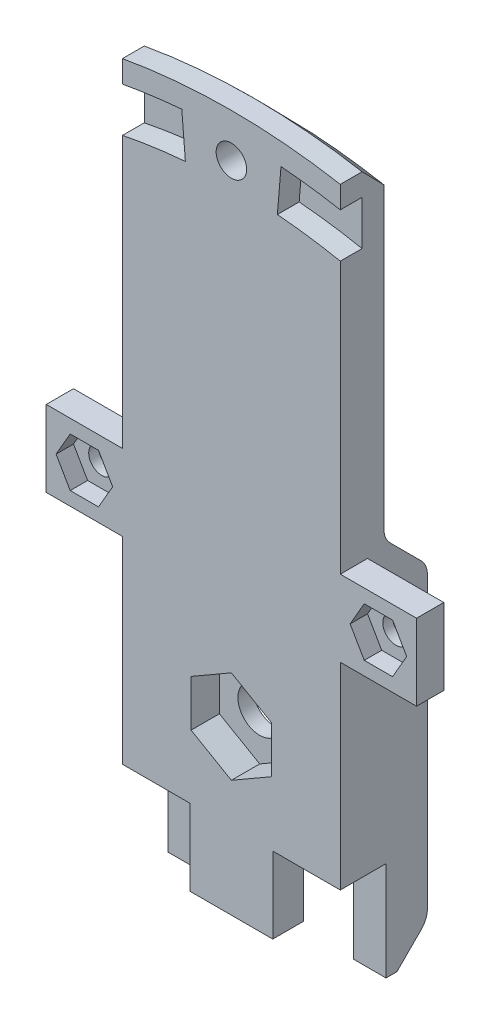
SolidWorks part; units mm, degrees
ref_plane "Front Plane" through (0, 0, 0) normal (0, 0, 1) x (1, 0, 0)
ref_plane "Top Plane" through (0, 0, 0) normal (0, 1, 0) x (1, 0, 0)
ref_plane "Right Plane" through (0, 0, 0) normal (1, 0, 0) x (0, 0, -1)
sketch "Sketch1" plane through (0, 0, 0) normal (0, 0, 1) x (1, 0, 0)
  line L0 (-12.7, -71.2673) -> (-12.7, 71.2673)
  line L1 (12.7, 71.2673) -> (12.7, -71.2673)
  line L2 (-12.7, 0) -> (12.7, 0)
  line L3 (0, 0) -> (0, 40.2261) construction
  arc A0 (-12.7, -71.2673) -> (12.7, -71.2673) centre (0, 0) ccw
  arc A1 (12.7, 71.2673) -> (-12.7, 71.2673) centre (0, 0) ccw
  circle A2 centre (0, 11.43) radius 7.62 construction
  dimension "D1" = 144.78
  dimension "D4" = 15.24
  dimension "D2" = 25.4
  dimension "D3" = 11.43
extrude "Boss-Extrude1" add sketch "Sketch1" along normal blind 5.08 contours L1 A1 L0 L2
sketch "Sketch2" plane through (0, 0, 5.08) normal (0, 0, 1) x (1, 0, 0)
  line L0 (-12.7, 0) -> (12.7, 0) construction
  line L1 (12.7, 71.2673) -> (12.7, 0) construction
  line L2 (-12.7, 0) -> (12.7, 0)
  circle A0 centre (0, 10.16) radius 2.54
extrude "Cut-Extrude1" cut sketch "Sketch2" against normal through all contours A0
sketch "Sketch3" plane through (0, 0, 5.08) normal (0, 0, 1) x (1, 0, 0)
  line L0 (-12.7, 0) -> (-12.7, 71.2673) construction
  line L1 (0, 15.5859) -> (-4.699, 12.873)
  line L2 (-4.699, 12.873) -> (-4.699, 7.447)
  line L3 (-4.699, 7.447) -> (0, 4.7341)
  line L4 (0, 4.7341) -> (4.699, 7.447)
  line L5 (4.699, 7.447) -> (4.699, 12.873)
  line L6 (4.699, 12.873) -> (0, 15.5859)
  circle A0 centre (0, 10.16) radius 4.699 construction
  dimension "D1" = 9.398
extrude "Cut-Extrude2" cut sketch "Sketch3" against normal blind 3.302
sketch "Sketch4" plane through (-12.7, 0, 0) normal (-1, 0, 0) x (0, 0, 1)
  line L0 (-0.7439, 32.1399) -> (-4.3361, 28.5478)
  line L1 (0, 0) -> (0, 71.2673) construction
  line L2 (-5.08, 26.7517) -> (-5.08, -6.9415)
  line L6 (-0.254, -11.5497) -> (-1.524, -11.5497)
  line L7 (0, 33.9359) -> (0, 0)
  line L8 (-1.524, -11.5497) -> (-4.3361, -8.7376)
  line L9 (0, 0) -> (-0.254, 0)
  line L10 (-0.254, 0) -> (-0.254, -11.5497)
  arc A0 (-4.3361, 28.5478) -> (-5.08, 26.7517) centre (-2.54, 26.7517) ccw
  arc A1 (0, 33.9359) -> (-0.7439, 32.1399) centre (-2.54, 33.9359) cw
  arc A2 (-5.08, -6.9415) -> (-4.3361, -8.7376) centre (-2.54, -6.9415) ccw
  point P15 (0, 31.75)
  dimension "D6" = 2.54
  dimension "D7" = 2.54
  dimension "D9" = 2.54
  dimension "D1" = 45
  dimension "D2" = 8.7376
  dimension "D3" = 45
  dimension "D4" = 1.27
  dimension "D5" = 5.08
  dimension "D8" = 33.9359
  dimension "D10" = 0.254
extrude "Boss-Extrude2" add sketch "Sketch4" against normal up to surface (25.4 mm away) up to face at (12.7, 35.6336, 2.54)
sketch "Sketch5" plane through (0, 0, 0) normal (1, 0, 0) x (0, 0, -1)
  line L0 (0, 33.9359) -> (0, -14.8745)
  line L1 (5.08, 24.709) -> (0, 22.86)
  line L2 (0, 22.86) -> (0, 0)
  line L9 (0, 33.9359) -> (0, 71.2673)
  line L10 (0, 71.2673) -> (-5.08, 71.2673)
  line L11 (-5.08, 71.2673) -> (-5.08, 0)
  line L12 (-5.08, 0) -> (0.254, 0)
  line L13 (0.254, 0) -> (0.254, -11.5497)
  line L14 (0.254, -11.5497) -> (1.524, -11.5497)
  line L15 (0.254, -11.5497) -> (1.524, -11.5497)
  line L16 (5.08, -6.9415) -> (5.08, 26.7517)
  line L17 (4.3361, 28.5478) -> (0.7439, 32.1399)
  line L18 (0, 33.9359) -> (0, 71.2673)
  line L19 (0, 71.2673) -> (-5.08, 71.2673)
  line L20 (-5.08, 71.2673) -> (-5.08, 0)
  line L21 (-5.08, 0) -> (0.254, 0)
  line L25 (5.08, -6.9415) -> (5.08, 26.7517)
  line L26 (4.3361, 28.5478) -> (0.7439, 32.1399)
  line L29 (1.524, -11.5497) -> (4.3361, -8.7376)
  line L30 (1.524, -11.5497) -> (4.3361, -8.7376)
  line L31 (0.254, 0) -> (0.254, -11.5497)
  arc A2 (5.08, 26.7517) -> (4.3361, 28.5478) centre (2.54, 26.7517) ccw
  arc A3 (0, 33.9359) -> (0.7439, 32.1399) centre (2.54, 33.9359) ccw
  arc A4 (5.08, 26.7517) -> (4.3361, 28.5478) centre (2.54, 26.7517) ccw
  arc A5 (0, 33.9359) -> (0.7439, 32.1399) centre (2.54, 33.9359) ccw
  arc A7 (4.3361, -8.7376) -> (5.08, -6.9415) centre (2.54, -6.9415) ccw
  arc A8 (4.3361, -8.7376) -> (5.08, -6.9415) centre (2.54, -6.9415) ccw
  dimension "D2" = 70
  dimension "D3" = 22.86
  dimension "D1" = 0
extrude "Cut-Extrude3" cut sketch "Sketch5" against normal mid plane 17.78
chamfer "Chamfer1" distance 2.54 angle 45 1 edges at (0, 72.39, 0)
sketch "Sketch6" plane through (0, 0, 5.08) normal (0, 0, 1) x (1, 0, 0)
  line L0 (-12.7, 0) -> (12.7, 0) construction
  line L1 (-4.826, 0) -> (4.826, 0)
  line L2 (-4.826, 0) -> (-4.826, -8.89)
  line L3 (-4.826, -8.89) -> (4.826, -8.89)
  line L4 (4.826, 0) -> (4.826, -8.89)
  line L5 (-4.826, 0) -> (4.826, -8.89) construction
  line L6 (-4.826, -8.89) -> (4.826, 0) construction
  line L7 (-12.7, -11.5497) -> (-12.7, 0) construction
  line L8 (12.7, 71.2673) -> (12.7, 0) construction
  point P4 (0, -4.445)
extrude "Boss-Extrude3" add sketch "Sketch6" against normal blind 3.556
sketch "Sketch8" plane through (0, 0, 0) normal (0, 0, -1) x (-1, 0, 0)
  line L0 (-0.5228, 37.6298) -> (-0.5228, 106.6362) construction
  line L3 (-4.5278, 41.6168) -> (31.321, 41.6168) construction
  line L4 (-9.4837, 45.8216) -> (17.6963, 45.8216) construction
  line L5 (10.16, 33.9359) -> (10.16, 69.1071) construction
  line L6 (-12.7, 33.9359) -> (12.7, 33.9359) construction
  line L7 (-10.16, 33.9359) -> (-10.16, 69.1071) construction
  line L8 (-12.7, 68.6858) -> (-12.7, 33.9359) construction
  line L9 (12.7, 33.9359) -> (12.7, 68.6858) construction
  line L10 (5.715, 33.9359) -> (5.715, 69.6158) construction
  line L11 (-5.715, 69.6158) -> (-5.715, 33.9359) construction
  line L17 (10.033, 36.6029) -> (-10.033, 47.7789) construction
  line L18 (10.033, 47.7789) -> (-10.033, 36.6029) construction
  line L23 (-10.795, 48.5409) -> (10.795, 35.8409) construction
  line L24 (-10.795, 35.8409) -> (10.795, 48.5409) construction
  arc A0 (12.7, 68.6858) -> (-12.7, 68.6858) centre (0, 0) ccw construction
  text T0 "<b>SSS</b>\r\n\r\n" font "Swis721 Blk BT" height 3.81
  text T1 "<b>UC Davis</b>"
  point P29 (0, 42.1909)
  point P34 (0, 42.1909)
extrude "Cut-Extrude4" cut sketch "Sketch8" against normal blind 0.508
sketch "Sketch9" plane through (0, 0, 0) normal (0, 0, -1) x (-1, 0, 0)
  line L0 (-12.7, 68.6858) -> (-12.7, 33.9359) construction
  line L1 (-10.033, 47.7789) -> (10.033, 47.7789)
  line L2 (-10.033, 47.7789) -> (-10.033, 36.6029)
  line L3 (-10.033, 36.6029) -> (10.033, 36.6029)
  line L4 (10.033, 47.7789) -> (10.033, 36.6029)
  line L5 (-10.033, 47.7789) -> (10.033, 36.6029) construction
  line L6 (-10.033, 36.6029) -> (10.033, 47.7789) construction
  line L7 (-10.795, 48.5409) -> (10.795, 48.5409)
  line L8 (-10.795, 48.5409) -> (-10.795, 35.8409)
  line L9 (-10.795, 35.8409) -> (10.795, 35.8409)
  line L10 (10.795, 48.5409) -> (10.795, 35.8409)
  line L11 (-10.795, 48.5409) -> (10.795, 35.8409) construction
  line L12 (-10.795, 35.8409) -> (10.795, 48.5409) construction
  line L13 (12.7, 33.9359) -> (12.7, 68.6858) construction
  line L14 (-12.7, 33.9359) -> (12.7, 33.9359) construction
  point P4 (0, 42.1909)
  point P9 (0, 42.1909)
extrude "Cut-Extrude5" cut sketch "Sketch9" against normal up to surface (0.508 mm away) up to face at (2.7572, 44.6416, 0.508)
sketch "Sketch10" plane through (0, 0, 0) normal (0, 0, -1) x (-1, 0, 0)
  line L0 (14.5022, 72.39) -> (-13.2786, 72.39) construction
  line L1 (12.7, 60.3434) -> (-12.7, 60.3434) construction
  line L2 (12.7, 33.9359) -> (12.7, 68.6858) construction
  line L3 (-12.7, 68.6858) -> (-12.7, 33.9359) construction
  circle A0 centre (0, 67.31) radius 4.953
  arc A2 (12.7, 71.2673) -> (-12.7, 71.2673) centre (0, 0) ccw construction
  arc A3 (12.7, 71.2673) -> (-12.7, 71.2673) centre (0, 0) ccw
  arc M8 (12.7, 68.6858) -> (-12.7, 68.6858) centre (0, 0) ccw
extrude "Cut-Extrude6" cut sketch "Sketch10" against normal blind 2.54 contours A0 M8 | A0 M8
sketch "Sketch11" plane through (0, 0, 2.54) normal (0, 0, -1) x (-1, 0, 0)
  circle A0 centre (0, 67.31) radius 1.778
  dimension "D1" = 3.556
extrude "Cut-Extrude7" cut sketch "Sketch11" against normal through all
sketch "Sketch12" plane through (0, 0, 5.08) normal (0, 0, 1) x (1, 0, 0)
  line L4 (12.7, 71.2673) -> (12.7, 0) construction
  line L5 (-12.7, 0) -> (-12.7, 71.2673) construction
  line L6 (0, 0) -> (-5.7842, 69.6101) construction
  line L7 (0, 0) -> (5.7842, 69.6101) construction
  line L8 (0, 69.85) -> (0, 0) construction
  line L9 (-5.7842, 69.6101) -> (-5.3635, 64.5475)
  line L10 (5.7842, 69.6101) -> (5.3635, 64.5475)
  line L11 (-12.7, 68.6858) -> (-12.7, 63.5127)
  line L12 (12.7, 63.5127) -> (12.7, 68.6858)
  arc A1 (12.7, 68.6858) -> (5.7842, 69.6101) centre (0, 0) ccw
  arc A2 (12.7, 63.5127) -> (5.3635, 64.5475) centre (0, 0) ccw
  arc A3 (-5.3635, 64.5475) -> (-12.7, 63.5127) centre (0, 0) ccw
  arc A4 (-5.7842, 69.6101) -> (-12.7, 68.6858) centre (0, 0) ccw
extrude "Cut-Extrude8" cut sketch "Sketch12" against normal blind 2.54
sketch "Sketch13" plane through (0, 0, 5.08) normal (0, 0, 1) x (1, 0, 0)
  line L0 (12.7, 63.5127) -> (12.7, 0) construction
  line L1 (12.7, 31.8973) -> (21.59, 31.8973)
  line L2 (12.7, 31.8973) -> (12.7, 23.0073)
  line L3 (12.7, 23.0073) -> (21.59, 23.0073)
  line L4 (21.59, 31.8973) -> (21.59, 23.0073)
  line L5 (12.7, 31.8973) -> (21.59, 23.0073) construction
  line L6 (12.7, 23.0073) -> (21.59, 31.8973) construction
  line L7 (-12.7, 0) -> (-12.7, 63.5127) construction
  line L8 (-12.7, 31.8973) -> (-21.59, 31.8973)
  line L9 (-12.7, 31.8973) -> (-12.7, 23.0073)
  line L10 (-12.7, 23.0073) -> (-21.59, 23.0073)
  line L11 (-21.59, 31.8973) -> (-21.59, 23.0073)
  line L12 (-12.7, 31.8973) -> (-21.59, 23.0073) construction
  line L13 (-12.7, 23.0073) -> (-21.59, 31.8973) construction
  circle A0 centre (-17.145, 27.4523) radius 1.524
  circle A1 centre (17.145, 27.4523) radius 1.524
  point P4 (17.145, 27.4523)
  point P11 (-17.145, 27.4523)
extrude "Boss-Extrude4" add sketch "Sketch13" against normal blind 3.175
sketch "Sketch14" plane through (0, 0, 5.08) normal (0, 0, 1) x (1, 0, 0)
  line L1 (-15.4952, 30.3098) -> (-18.7948, 30.3098)
  line L2 (-18.7948, 30.3098) -> (-20.4446, 27.4523)
  line L3 (-20.4446, 27.4523) -> (-18.7948, 24.5948)
  line L4 (-18.7948, 24.5948) -> (-15.4952, 24.5948)
  line L5 (-15.4952, 24.5948) -> (-13.8454, 27.4523)
  line L6 (-13.8454, 27.4523) -> (-15.4952, 30.3098)
  line L7 (18.7948, 30.3098) -> (15.4952, 30.3098)
  line L8 (15.4952, 30.3098) -> (13.8454, 27.4523)
  line L9 (13.8454, 27.4523) -> (15.4952, 24.5948)
  line L10 (15.4952, 24.5948) -> (18.7948, 24.5948)
  line L11 (18.7948, 24.5948) -> (20.4446, 27.4523)
  line L12 (20.4446, 27.4523) -> (18.7948, 30.3098)
  circle A0 centre (-17.145, 27.4523) radius 2.8575 construction
  circle A1 centre (17.145, 27.4523) radius 2.8575 construction
  dimension "D1" = 5.715
extrude "Cut-Extrude9" cut sketch "Sketch14" against normal blind 2.032
equation "\"D3@Sketch2\"=\"D4@Sketch2\"/2"
equation "\"D2@Sketch6\"=\"D3@Sketch6\""
equation "\"D2@Sketch8\"=\"D1@Sketch8\""
equation "\"D3@Sketch8\"=\"D4@Sketch8\""
equation "\"D2@Sketch9\"=\"D1@Sketch9\""
equation "\"D3@Sketch9\"=\"D1@Sketch9\""
equation "\"D5@Sketch9\"=\"D4@Sketch9\""
equation "\"D4@Sketch10\"=\"D3@Sketch10\"/2"
equation "\"D4@Sketch12\"=\"D3@Sketch12\"/2"
equation "\"D4@Sketch13\"=\"D3@Sketch13\""
